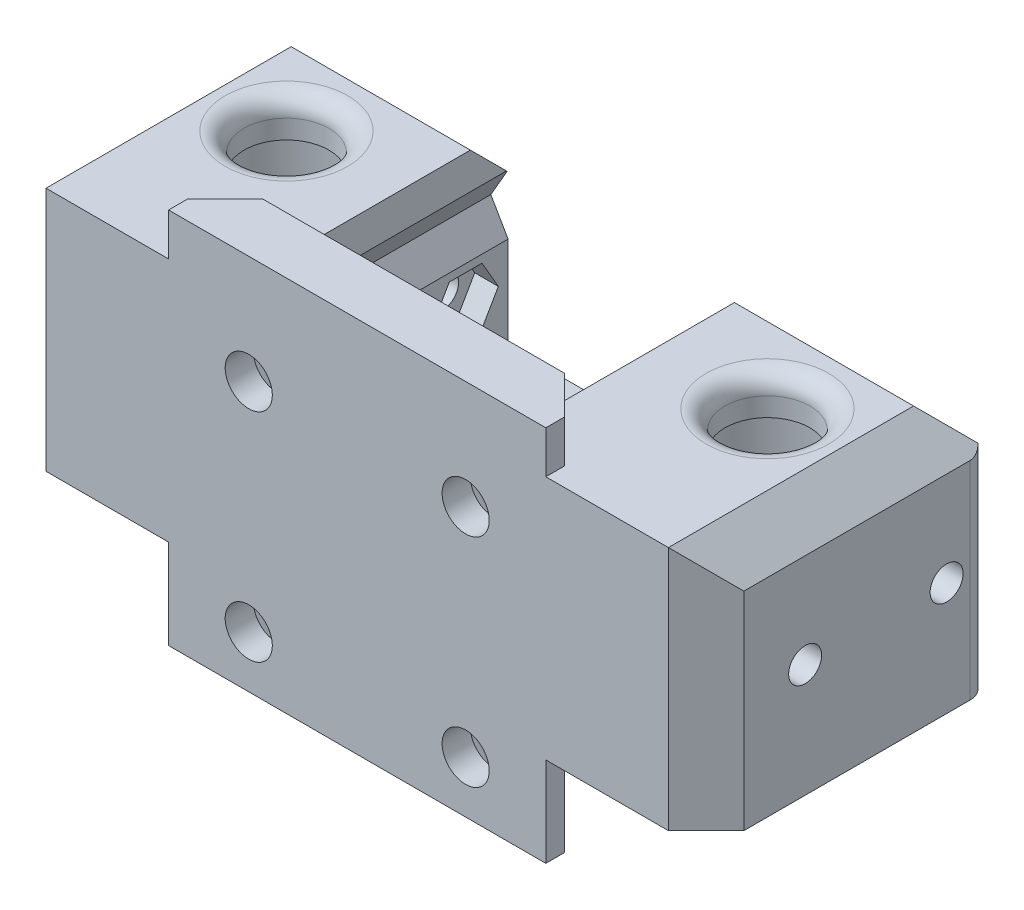
SolidWorks part; units mm, degrees
ref_plane "Plan de face" through (0, 0, 0) normal (0, 0, 1) x (1, 0, 0)
ref_plane "Plan de dessus" through (0, 0, 0) normal (0, 1, 0) x (1, 0, 0)
ref_plane "Plan de droite" through (0, 0, 0) normal (1, 0, 0) x (0, 0, -1)
sketch "Esquisse1" plane through (0, 0, 0) normal (0, 0, 1) x (1, 0, 0)
  line L0 (0, 0) -> (0, 33.886) construction
  line L1 (-20, 20) -> (0, 20)
  line L2 (-20, 20) -> (-20, -20)
  line L3 (-20, -20) -> (0, -20)
  line L4 (0, 20) -> (0, -20)
  line L5 (-20, 20) -> (0, -20) construction
  line L6 (-20, -20) -> (0, 20) construction
  point P0 (-10, 0)
  dimension "D1" = 40
  dimension "D2" = 40
extrude "Boss.-Extru.1" add sketch "Esquisse1" along normal blind 6
ref_plane "Plan1" through (0, -10.5, 0) normal (0, -1, 0) x (-1, 0, 0)
sketch "Esquisse2" plane through (0, -10.5, 0) normal (0, -1, 0) x (-1, 0, 0)
  line L0 (20, -6) -> (0, -6) construction
  line L1 (-17, 24) -> (20, 24)
  line L2 (-17, 24) -> (-17, -6)
  line L3 (-17, -6) -> (20, -6)
  line L4 (20, 24) -> (20, -6)
  line L5 (-17, 24) -> (20, -6) construction
  line L6 (-17, -6) -> (20, 24) construction
  line L8 (0, 0) -> (20, 0) construction
  point P0 (1.5, 9)
  dimension "D1" = 30
  dimension "D2" = 37
  dimension "D3" = 20
extrude "Boss.-Extru.2" add sketch "Esquisse2" against normal blind 6
sketch "Esquisse3" plane through (0, -4.5, 0) normal (0, 1, 0) x (1, 0, 0)
  line L1 (-6, 24) -> (17, 24)
  line L2 (-6, 24) -> (-6, -6)
  line L3 (-6, -6) -> (17, -6)
  line L4 (17, 24) -> (17, -6)
  line L5 (-6, 24) -> (17, -6) construction
  line L6 (-6, -6) -> (17, 24) construction
  line L8 (17, 24) -> (17, -6) construction
  line L9 (-20, 24) -> (17, 24) construction
  line L10 (17, -6) -> (0, -6) construction
  point P0 (5.5, 9)
  dimension "D1" = 23
extrude "Boss.-Extru.3" add sketch "Esquisse3" along normal blind 20
sketch "Esquisse4" plane through (0, -10.5, 0) normal (0, -1, 0) x (-1, 0, 0)
  line L2 (-17, 24) -> (6, 24) construction
  line L3 (-5.5, 24) -> (-5.5, 0) construction
  line L6 (0, 0) -> (-17, 0) construction
  line L7 (-17, 24) -> (-17, -6) construction
  circle A0 centre (-5.5, 12) radius 9.25
  dimension "D1" = 18.5
extrude "Enlèv. mat.-Extru.1" cut sketch "Esquisse4" against normal blind 8
sketch "Esquisse5" plane through (0, -2.5, 0) normal (0, -1, 0) x (-1, 0, 0)
  circle A0 centre (-5.5, 12) radius 8.25
  dimension "D1" = 16.5
extrude "Enlèv. mat.-Extru.2" cut sketch "Esquisse5" against normal blind 14
sketch "Esquisse6" plane through (0, 11.5, 0) normal (0, -1, 0) x (-1, 0, 0)
  circle A0 centre (-5.5, 12) radius 4.5
  dimension "D1" = 9
extrude "Enlèv. mat.-Extru.3" cut sketch "Esquisse6" against normal blind 4
sketch "Esquisse9" plane through (17, 0, 0) normal (1, 0, 0) x (0, 0, -1)
  line L0 (4.5, 1.5) -> (19.5, 1.5) construction
  line L1 (0, 0) -> (0, 15.5) construction
  line L2 (-6, 15.5) -> (24, 15.5) construction
  line L3 (24, 1.5) -> (0, 1.5) construction
  line L4 (24, 15.5) -> (24, -10.5) construction
  line L5 (24, -10.5) -> (-6, -10.5) construction
  circle A0 centre (4.5, 1.5) radius 1.75
  circle A1 centre (19.5, 1.5) radius 1.75
  point P4 (12, 1.5)
  dimension "D2" = 3.5
  dimension "D1" = 15
  dimension "D3" = 12
extrude "Enlèv. mat.-Extru.5" cut sketch "Esquisse9" against normal up to surface (23 mm away) up to face at (-6, 5.5, -12)
sketch "Esquisse11" plane through (-6, 0, 0) normal (-1, 0, 0) x (0, 0, 1)
  line L1 (-17.7679, -1.5) -> (-16.0359, 1.5)
  line L2 (-16.0359, 1.5) -> (-17.7679, 4.5)
  line L3 (-17.7679, 4.5) -> (-21.2321, 4.5)
  line L4 (-21.2321, 4.5) -> (-22.9641, 1.5)
  line L5 (-22.9641, 1.5) -> (-21.2321, -1.5)
  line L6 (-21.2321, -1.5) -> (-17.7679, -1.5)
  line L7 (-2.7679, -1.5) -> (-1.0359, 1.5)
  line L8 (-1.0359, 1.5) -> (-2.7679, 4.5)
  line L9 (-2.7679, 4.5) -> (-6.2321, 4.5)
  line L10 (-6.2321, 4.5) -> (-7.9641, 1.5)
  line L11 (-7.9641, 1.5) -> (-6.2321, -1.5)
  line L12 (-6.2321, -1.5) -> (-2.7679, -1.5)
  circle A0 centre (-19.5, 1.5) radius 3 construction
  circle A1 centre (-4.5, 1.5) radius 3 construction
  dimension "D1" = 6
extrude "Enlèv. mat.-Extru.7" cut sketch "Esquisse11" against normal blind 2.5
chamfer "Chanfrein1" distance 4 angle 45 5 edges at (5.5, 15.5, -24) (0, -15.25, 0) (17, 15.5, -9) (17, 2.5, 6) (0, 17.75, 0)
fillet "Congé2" radius 2 2 edges at (5.5, 15.5, -16.5) (17, 0.5, -24)
mirror "Symétrie1" about plane through (-20, 20, 6) normal (1, 0, 0) of bodies 111 108
sketch "Esquisse10" plane through (0, 0, 6) normal (0, 0, 1) x (1, 0, 0)
  line L0 (-20, 20) -> (-20, -20) construction
  line L1 (-31.5, 8.5) -> (-8.5, 8.5) construction
  line L2 (-31.5, 8.5) -> (-31.5, -14.5) construction
  line L3 (-31.5, -14.5) -> (-8.5, -14.5) construction
  line L4 (-8.5, 8.5) -> (-8.5, -14.5) construction
  line L5 (-31.5, 8.5) -> (-8.5, -14.5) construction
  line L6 (-31.5, -14.5) -> (-8.5, 8.5) construction
  line L7 (0, 20) -> (-40, 20) construction
  line L8 (-40, -20) -> (0, -20) construction
  circle A0 centre (-31.5, 8.5) radius 2.5
  circle A1 centre (-8.5, 8.5) radius 2.5
  circle A2 centre (-8.5, -14.5) radius 2.5
  circle A3 centre (-31.5, -14.5) radius 2.5
  point P0 (-20, -3)
  dimension "D3" = 5
  dimension "D1" = 23
  dimension "D2" = 23
  dimension "D4" = 23
extrude "Enlèv. mat.-Extru.6" cut sketch "Esquisse10" against normal through all
sketch "Esquisse12" plane through (0, 0, 0) normal (0, 0, -1) x (-1, 0, 0)
  line L1 (10.6651, 4.75) -> (12.8301, 8.5)
  line L2 (12.8301, 8.5) -> (10.6651, 12.25)
  line L3 (10.6651, 12.25) -> (6.3349, 12.25)
  line L4 (6.3349, 12.25) -> (4.1699, 8.5)
  line L5 (4.1699, 8.5) -> (6.3349, 4.75)
  line L6 (6.3349, 4.75) -> (10.6651, 4.75)
  line L7 (33.6651, 4.75) -> (35.8301, 8.5)
  line L8 (35.8301, 8.5) -> (33.6651, 12.25)
  line L9 (33.6651, 12.25) -> (29.3349, 12.25)
  line L10 (29.3349, 12.25) -> (27.1699, 8.5)
  line L11 (27.1699, 8.5) -> (29.3349, 4.75)
  line L12 (29.3349, 4.75) -> (33.6651, 4.75)
  line L13 (10.6651, -18.25) -> (12.8301, -14.5)
  line L14 (12.8301, -14.5) -> (10.6651, -10.75)
  line L15 (10.6651, -10.75) -> (6.3349, -10.75)
  line L16 (6.3349, -10.75) -> (4.1699, -14.5)
  line L17 (4.1699, -14.5) -> (6.3349, -18.25)
  line L18 (6.3349, -18.25) -> (10.6651, -18.25)
  line L19 (33.6651, -18.25) -> (35.8301, -14.5)
  line L20 (35.8301, -14.5) -> (33.6651, -10.75)
  line L21 (33.6651, -10.75) -> (29.3349, -10.75)
  line L22 (29.3349, -10.75) -> (27.1699, -14.5)
  line L23 (27.1699, -14.5) -> (29.3349, -18.25)
  line L24 (29.3349, -18.25) -> (33.6651, -18.25)
  circle A0 centre (8.5, 8.5) radius 3.75 construction
  circle A1 centre (31.5, 8.5) radius 3.75 construction
  circle A2 centre (8.5, -14.5) radius 3.75 construction
  circle A3 centre (31.5, -14.5) radius 3.75 construction
  dimension "D1" = 7.5
extrude "Enlèv. mat.-Extru.8" cut sketch "Esquisse12" against normal blind 3 and the other way through all
